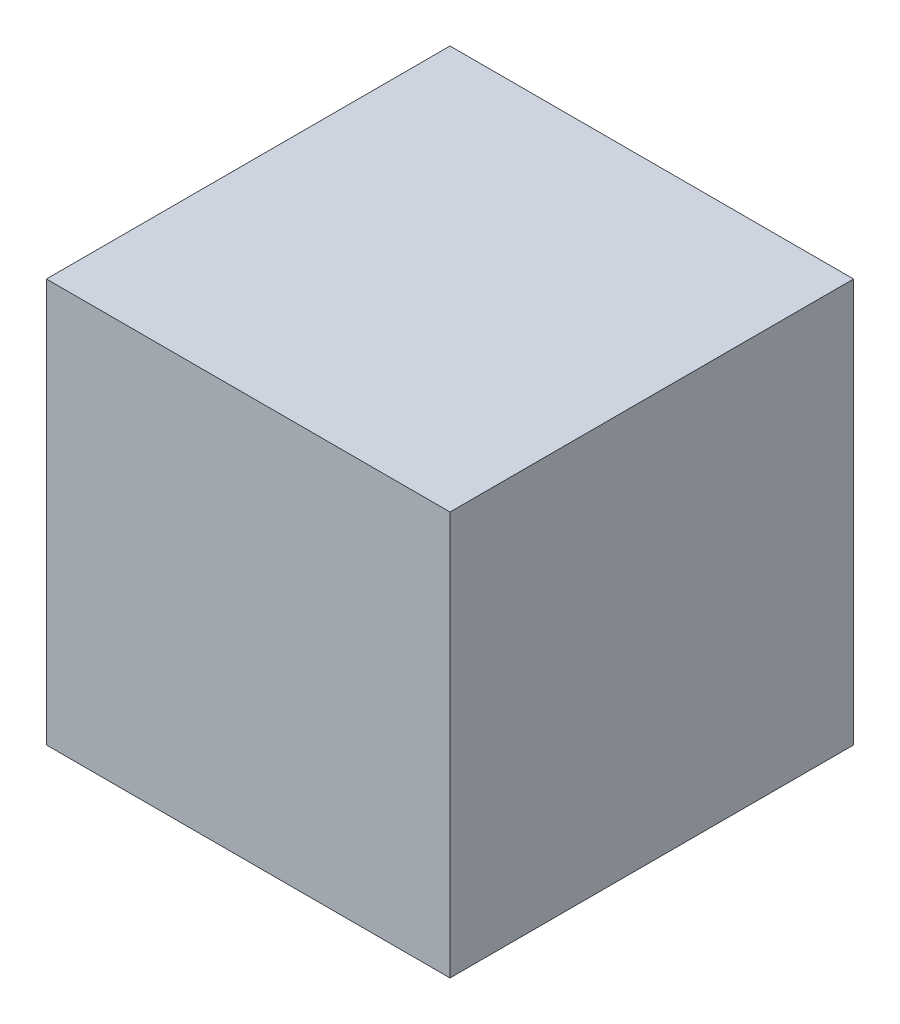
SolidWorks part; units mm, degrees
ref_plane "Front Plane" through (0, 0, 0) normal (0, 0, 1) x (1, 0, 0)
ref_plane "Top Plane" through (0, 0, 0) normal (0, 1, 0) x (1, 0, 0)
ref_plane "Right Plane" through (0, 0, 0) normal (1, 0, 0) x (0, 0, -1)
sketch "Sketch1" plane through (0, 0, 0) normal (0, 1, 0) x (1, 0, 0)
  line L1 (-28.25, -28.25) -> (28.25, -28.25)
  line L2 (-28.25, -28.25) -> (-28.25, 28.25)
  line L3 (-28.25, 28.25) -> (28.25, 28.25)
  line L4 (28.25, -28.25) -> (28.25, 28.25)
  line L5 (-28.25, -28.25) -> (28.25, 28.25) construction
  line L6 (-28.25, 28.25) -> (28.25, -28.25) construction
  point P0 (0, 0)
  dimension "D1" = 56.5
  dimension "D2" = 56.5
extrude "Boss-Extrude1" add sketch "Sketch1" along normal mid plane 56.5
sketch "Sketch2" plane through (0, 28.25, 0) normal (0, 1, 0) x (1, 0, 0)
  line L0 (-9.42, 28.25) -> (-9.42, -28.25)
  line L1 (28.25, 28.25) -> (-28.25, 28.25) construction
  line L2 (-28.25, -28.25) -> (28.25, -28.25) construction
  line L3 (9.42, 28.25) -> (9.42, -28.25)
  line L4 (-28.25, 9.42) -> (28.25, 9.42)
  line L5 (-28.25, 28.25) -> (-28.25, -28.25) construction
  line L6 (28.25, -28.25) -> (28.25, 28.25) construction
  line L7 (-28.25, -9.42) -> (28.25, -9.42)
  dimension "D1" = 18.83
  dimension "D2" = 18.83
  dimension "D3" = 18.83
  dimension "D4" = 18.83
  dimension "D5" = 18.84
sketch "Sketch4" plane through (0, 0, 28.25) normal (0, 0, 1) x (1, 0, 0)
  line L0 (-9.42, -28.25) -> (-9.42, 28.25)
  line L1 (-28.25, -28.25) -> (28.25, -28.25) construction
  line L2 (-28.25, 28.25) -> (28.25, 28.25) construction
  line L3 (9.42, 28.25) -> (9.42, -28.25)
  line L4 (-28.25, 9.42) -> (28.25, 9.42)
  line L5 (-28.25, 28.25) -> (-28.25, -28.25) construction
  line L6 (28.25, 28.25) -> (28.25, -28.25) construction
  line L7 (-28.25, -9.42) -> (28.25, -9.42)
  line L8 (0, 0) -> (-202.8372, 0) construction
  dimension "D1" = 18.83
  dimension "D2" = 18.83
  dimension "D3" = 18.83
  dimension "D4" = 18.83
